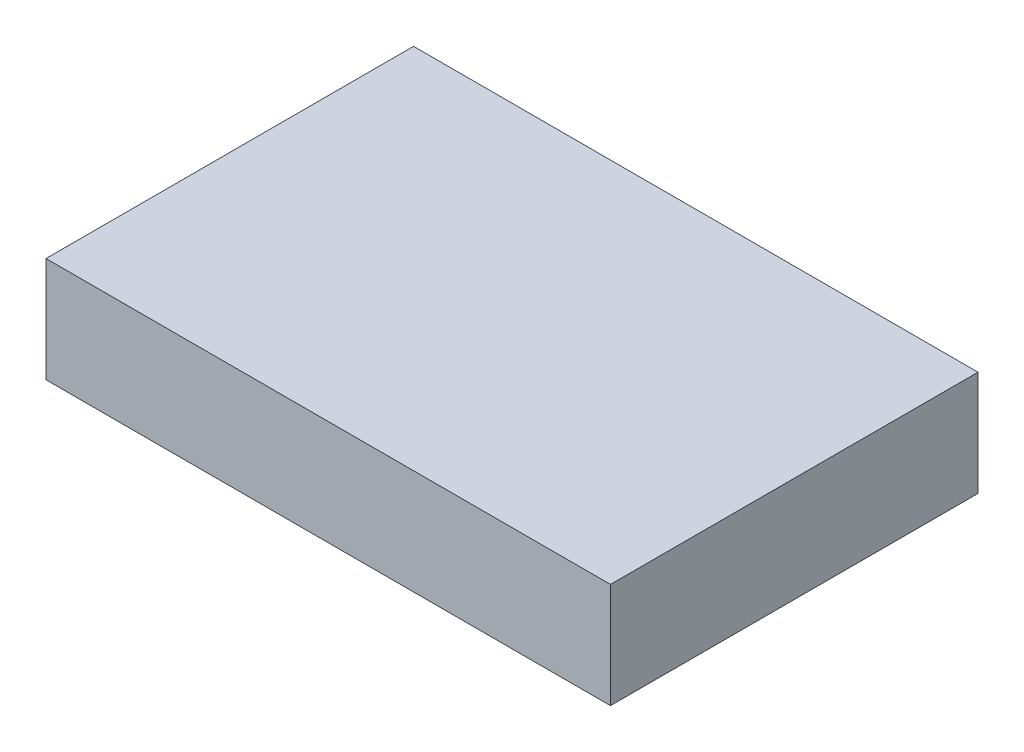
SolidWorks part; units mm, degrees
ref_plane "Front Plane" through (0, 0, 0) normal (0, 0, 1) x (1, 0, 0)
ref_plane "Top Plane" through (0, 0, 0) normal (0, 1, 0) x (1, 0, 0)
ref_plane "Right Plane" through (0, 0, 0) normal (1, 0, 0) x (0, 0, -1)
sketch "Sketch1" plane through (0, 0, 0) normal (0, 1, 0) x (1, 0, 0)
  line L1 (-68.2625, -44.45) -> (68.2625, -44.45)
  line L2 (-68.2625, -44.45) -> (-68.2625, 44.45)
  line L3 (-68.2625, 44.45) -> (68.2625, 44.45)
  line L4 (68.2625, -44.45) -> (68.2625, 44.45)
  line L5 (-68.2625, -44.45) -> (68.2625, 44.45) construction
  line L6 (-68.2625, 44.45) -> (68.2625, -44.45) construction
  point P0 (0, 0)
  dimension "D1" = 136.525
  dimension "D2" = 88.9
extrude "Boss-Extrude1" add sketch "Sketch1" along normal blind 25.4
